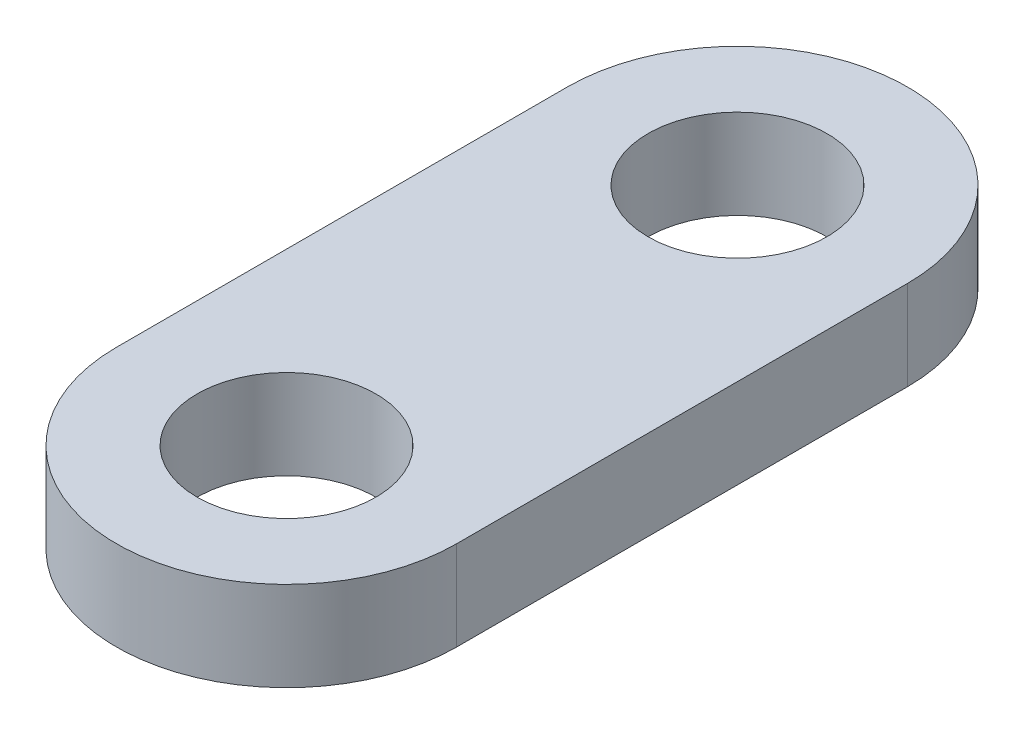
SolidWorks part; units mm, degrees
ref_plane "Front Plane" through (0, 0, 0) normal (0, 0, 1) x (1, 0, 0)
ref_plane "Top Plane" through (0, 0, 0) normal (0, 1, 0) x (1, 0, 0)
ref_plane "Right Plane" through (0, 0, 0) normal (1, 0, 0) x (0, 0, -1)
sketch "Sketch1" plane through (0, 0, 0) normal (0, 1, 0) x (1, 0, 0)
  line L0 (0, 6.5788) -> (0, -6.0212) construction
  line L1 (4.7529, 6.5788) -> (4.7529, -6.0212)
  line L2 (-4.7529, 6.5788) -> (-4.7529, -6.0212)
  circle A0 centre (0, 6.5788) radius 2.5
  circle A1 centre (0, -6.0212) radius 2.5
  arc A2 (4.7529, 6.5788) -> (-4.7529, 6.5788) centre (0, 6.5788) ccw
  arc A3 (-4.7529, -6.0212) -> (4.7529, -6.0212) centre (0, -6.0212) ccw
  point P4 (0, 0.2788)
  dimension "D2" = 5
  dimension "D3" = 5
  dimension "D1" = 12.6
extrude "Boss-Extrude1" add sketch "Sketch1" along normal blind 2.5
